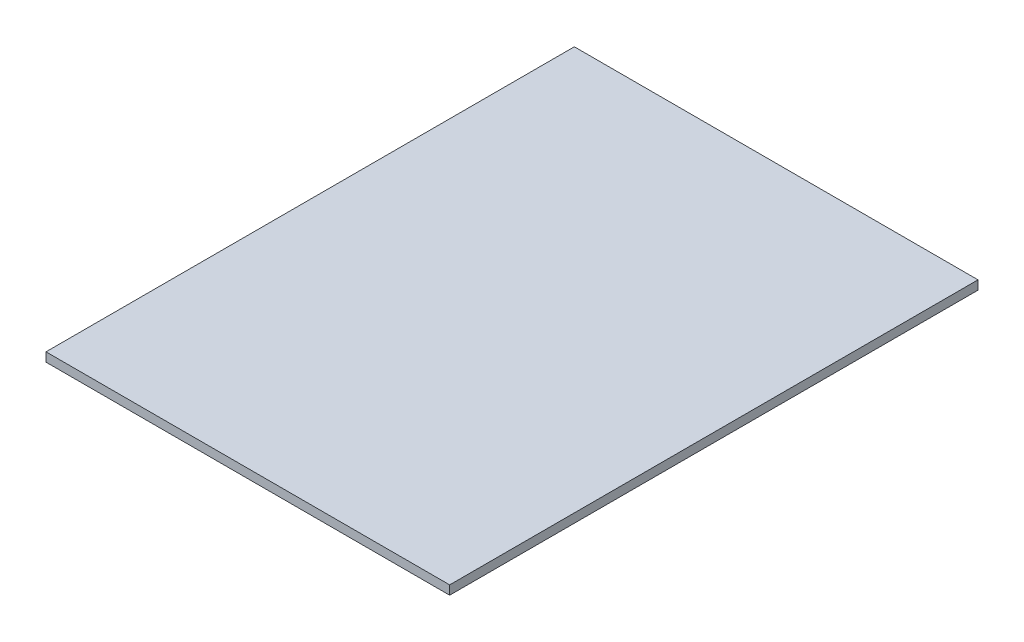
SolidWorks part; units mm, degrees
material "Plain Carbon Steel"
ref_plane "Front Plane" through (0, 0, 0) normal (0, 0, 1) x (1, 0, 0)
ref_plane "Top Plane" through (0, 0, 0) normal (0, 1, 0) x (1, 0, 0)
ref_plane "Right Plane" through (0, 0, 0) normal (1, 0, 0) x (0, 0, -1)
sketch "Sketch1" plane through (0, 0, 0) normal (0, 1, 0) x (1, 0, 0)
  line L1 (0, 0) -> (54, 0)
  line L2 (0, 0) -> (0, 70.68)
  line L3 (0, 70.68) -> (54, 70.68)
  line L4 (54, 0) -> (54, 70.68)
  dimension "D1" = 54
  dimension "D2" = 70.68
extrude "Boss-Extrude1" add sketch "Sketch1" along normal blind 1.2
